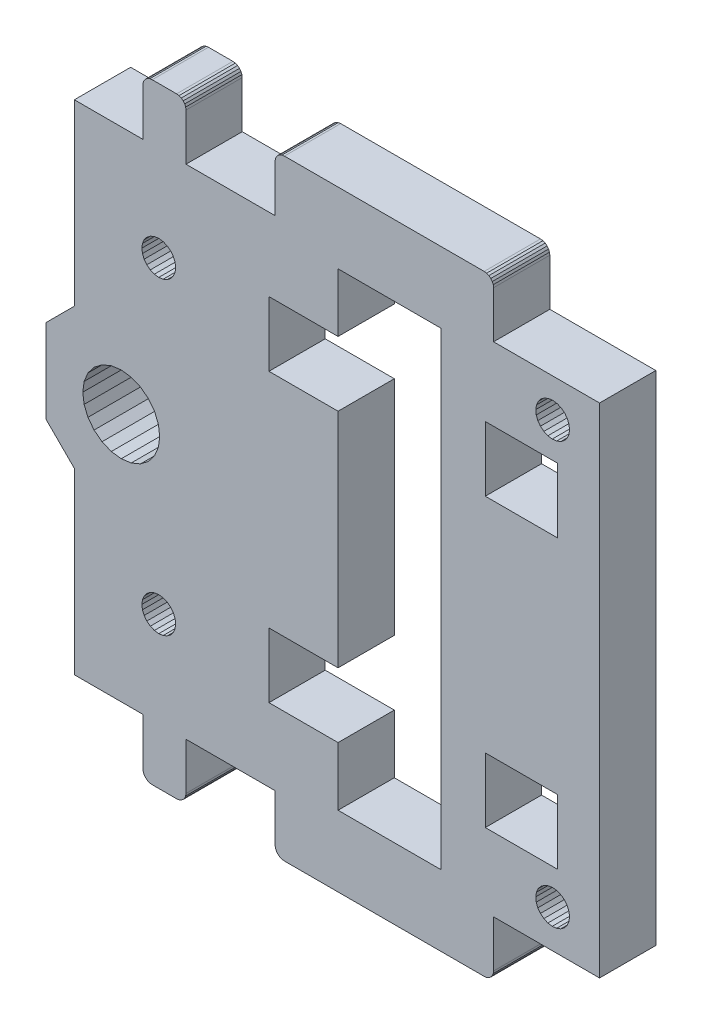
SolidWorks part; units mm, degrees
material "Maple"
ref_plane "Front Plane" through (0, 0, 0) normal (0, 0, 1) x (1, 0, 0)
ref_plane "Top Plane" through (0, 0, 0) normal (0, 1, 0) x (1, 0, 0)
ref_plane "Right Plane" through (0, 0, 0) normal (1, 0, 0) x (0, 0, -1)
sketch "Sketch1" plane through (0, 0, 0) normal (0, 0, 1) x (1, 0, 0)
  line L463 (-397.798, -104.5282) -> (-397.9876, -104.9582)
  line L464 (-397.9876, -104.9582) -> (-398.0594, -105.4226)
  line L465 (-398.0594, -105.4226) -> (-398.0086, -105.8897)
  line L466 (-398.0086, -105.8897) -> (-397.8386, -106.3278)
  line L467 (-397.8386, -106.3278) -> (-397.5611, -106.7069)
  line L468 (-397.5611, -106.7069) -> (-397.1948, -107.0013)
  line L469 (-397.1948, -107.0013) -> (-396.7648, -107.1909)
  line L470 (-396.7648, -107.1909) -> (-396.3005, -107.2627)
  line L471 (-396.3005, -107.2627) -> (-395.8333, -107.2119)
  line L472 (-395.8333, -107.2119) -> (-395.3953, -107.0419)
  line L473 (-395.3953, -107.0419) -> (-395.0161, -106.7643)
  line L474 (-395.0161, -106.7643) -> (-394.7217, -106.3981)
  line L475 (-394.7217, -106.3981) -> (-394.5322, -105.9681)
  line L476 (-394.5322, -105.9681) -> (-394.4603, -105.5037)
  line L477 (-394.4603, -105.5037) -> (-394.5112, -105.0366)
  line L478 (-425.7259, -95.9132) -> (-425.8258, -96.1543)
  line L479 (-439.92, -159.7726) -> (-439.82, -160.0136)
  line L480 (-439.82, -160.0136) -> (-439.661, -160.2205)
  line L481 (-439.661, -160.2205) -> (-439.454, -160.3793)
  line L482 (-446.3599, -127.9632) -> (-446.2202, -129.0243)
  line L483 (-438.2996, -129.0243) -> (-438.1599, -127.9632)
  line L484 (-443.321, -124.0029) -> (-444.3099, -124.4124)
  line L485 (-441.1987, -131.9234) -> (-440.2099, -131.5139)
  line L486 (-442.2599, -123.8632) -> (-443.321, -124.0029)
  line L487 (-440.2099, -124.4124) -> (-441.1987, -124.0029)
  line L488 (-438.7092, -130.0132) -> (-438.2996, -129.0243)
  line L489 (-450.2599, -132.4522) -> (-447.2599, -135.4522)
  line L490 (-450.2599, -123.4741) -> (-450.2599, -127.9351)
  line L491 (-450.2599, -123.4741) -> (-447.2599, -120.4741)
  line L492 (-447.2599, -120.4741) -> (-447.2599, -101.4132)
  line L493 (-403.0599, -95.5471) -> (-403.3011, -95.4472)
  line L494 (-402.594, -96.1543) -> (-402.6939, -95.9132)
  line L495 (-402.5599, -96.4132) -> (-402.594, -96.1543)
  line L496 (-439.217, -95.4472) -> (-438.9582, -95.4132)
  line L497 (-438.9582, -95.4132) -> (-436.3585, -95.4132)
  line L498 (-439.4582, -95.5471) -> (-439.217, -95.4472)
  line L499 (-425.8599, -159.5132) -> (-425.8599, -154.5132)
  line L500 (-425.8599, -159.5132) -> (-425.8258, -159.772)
  line L501 (-424.8599, -95.4132) -> (-425.1187, -95.4472)
  line L502 (-425.1187, -95.4472) -> (-425.3599, -95.5471)
  line L503 (-436.0996, -95.4472) -> (-436.3585, -95.4132)
  line L504 (-435.394, -159.772) -> (-435.4939, -160.0132)
  line L505 (-435.4939, -160.0132) -> (-435.6528, -160.2203)
  line L506 (-424.8599, -95.4132) -> (-403.5599, -95.4132)
  line L507 (-394.5112, -105.0366) -> (-394.6811, -104.5985)
  line L508 (-394.6811, -104.5985) -> (-394.9587, -104.2194)
  line L509 (-394.9587, -104.2194) -> (-395.325, -103.925)
  line L510 (-395.325, -103.925) -> (-395.7549, -103.7354)
  line L511 (-395.7549, -103.7354) -> (-396.2193, -103.6636)
  line L512 (-439.454, -160.3793) -> (-439.2129, -160.4791)
  line L513 (-439.2129, -160.4791) -> (-438.9542, -160.5132)
  line L514 (-403.3011, -95.4472) -> (-403.5599, -95.4132)
  line L515 (-395.0204, -151.7684) -> (-394.7248, -151.4031)
  line L516 (-394.7248, -151.4031) -> (-394.5338, -150.9738)
  line L517 (-394.5338, -150.9738) -> (-394.4605, -150.5097)
  line L518 (-394.4605, -150.5097) -> (-394.5098, -150.0424)
  line L519 (-394.5098, -150.0424) -> (-394.6783, -149.6037)
  line L520 (-394.6783, -149.6037) -> (-394.9546, -149.2237)
  line L521 (-394.9546, -149.2237) -> (-395.3199, -148.9281)
  line L522 (-395.3199, -148.9281) -> (-395.7492, -148.7371)
  line L523 (-395.7492, -148.7371) -> (-396.2134, -148.6638)
  line L524 (-396.2134, -148.6638) -> (-396.6807, -148.713)
  line L525 (-396.6807, -148.713) -> (-397.1193, -148.8816)
  line L526 (-397.1193, -148.8816) -> (-397.4994, -149.1579)
  line L527 (-397.4994, -149.1579) -> (-397.795, -149.5232)
  line L528 (-439.9986, -111.0473) -> (-440.0599, -111.5132)
  line L529 (-435.4924, -95.9132) -> (-435.6514, -95.706)
  line L530 (-435.6514, -95.706) -> (-435.8585, -95.5471)
  line L531 (-419.1424, -139.8132) -> (-419.1424, -116.1132)
  line L532 (-419.1424, -109.2132) -> (-419.1424, -102.9632)
  line L533 (-450.2636, -127.9632) -> (-450.2599, -127.9912)
  line L534 (-450.2599, -127.9912) -> (-450.2599, -132.4522)
  line L535 (-450.2599, -127.9351) -> (-450.2636, -127.9632)
  line L536 (-447.2599, -154.5132) -> (-447.2599, -135.4522)
  line L537 (-447.2599, -154.5132) -> (-439.9582, -154.5132)
  line L538 (-391.2599, -154.5132) -> (-402.5599, -154.5132)
  line L539 (-402.5599, -154.5132) -> (-402.5599, -159.5132)
  line L540 (-435.3599, -154.5132) -> (-435.3599, -159.5132)
  line L541 (-391.2599, -101.4132) -> (-391.2599, -154.5132)
  line L542 (-391.2599, -101.4132) -> (-402.5599, -101.4132)
  line L543 (-426.5109, -109.2132) -> (-426.5109, -116.1132)
  line L544 (-426.5109, -116.1132) -> (-419.1424, -116.1132)
  line L545 (-403.4424, -109.2132) -> (-403.4424, -116.1132)
  line L546 (-395.7424, -109.2132) -> (-403.4424, -109.2132)
  line L547 (-403.4424, -116.1132) -> (-395.7424, -116.1132)
  line L548 (-395.7424, -116.1132) -> (-395.7424, -109.2132)
  line L549 (-419.1424, -139.8132) -> (-426.5109, -139.8132)
  line L550 (-403.4424, -139.8132) -> (-403.4424, -146.7132)
  line L551 (-426.5109, -146.7132) -> (-419.1424, -146.7132)
  line L552 (-426.5109, -139.8132) -> (-426.5109, -146.7132)
  line L553 (-395.7424, -146.7132) -> (-395.7424, -139.8132)
  line L554 (-403.4424, -146.7132) -> (-395.7424, -146.7132)
  line L555 (-395.7424, -139.8132) -> (-403.4424, -139.8132)
  line L556 (-435.3599, -159.5132) -> (-435.394, -159.772)
  line L557 (-425.8258, -96.1543) -> (-425.8599, -96.4132)
  line L558 (-439.6653, -95.706) -> (-439.4582, -95.5471)
  line L559 (-439.8242, -95.9132) -> (-439.6653, -95.706)
  line L560 (-439.9241, -96.1543) -> (-439.8242, -95.9132)
  line L561 (-435.3925, -96.1543) -> (-435.4924, -95.9132)
  line L562 (-436.3599, -160.5132) -> (-438.9542, -160.5132)
  line L563 (-436.1011, -160.4791) -> (-436.3599, -160.5132)
  line L564 (-438.7258, -146.1518) -> (-438.2599, -146.2132)
  line L565 (-438.2599, -146.2132) -> (-437.794, -146.1518)
  line L566 (-437.794, -146.1518) -> (-437.3599, -145.972)
  line L567 (-437.3599, -145.972) -> (-436.9871, -145.6859)
  line L568 (-436.9871, -145.6859) -> (-436.701, -145.3132)
  line L569 (-436.701, -145.3132) -> (-436.5212, -144.879)
  line L570 (-436.5212, -144.879) -> (-436.4599, -144.4132)
  line L571 (-436.4599, -144.4132) -> (-436.5212, -143.9473)
  line L572 (-436.5212, -143.9473) -> (-436.701, -143.5132)
  line L573 (-436.701, -143.5132) -> (-436.9871, -143.1404)
  line L574 (-436.9871, -143.1404) -> (-437.3599, -142.8543)
  line L575 (-437.3599, -142.8543) -> (-437.794, -142.6745)
  line L576 (-437.794, -142.6745) -> (-438.2599, -142.6132)
  line L577 (-438.2599, -142.6132) -> (-438.7258, -142.6745)
  line L578 (-402.6939, -95.9132) -> (-402.8528, -95.706)
  line L579 (-435.6528, -160.2203) -> (-435.8599, -160.3792)
  line L580 (-435.8599, -160.3792) -> (-436.1011, -160.4791)
  line L581 (-402.5599, -101.4132) -> (-402.5599, -96.4132)
  line L582 (-447.2599, -101.4132) -> (-439.9582, -101.4132)
  line L583 (-425.8599, -101.4132) -> (-425.8599, -96.4132)
  line L584 (-436.701, -110.6132) -> (-436.9871, -110.2404)
  line L585 (-436.9871, -110.2404) -> (-437.3599, -109.9543)
  line L586 (-437.3599, -109.9543) -> (-437.794, -109.7745)
  line L587 (-437.794, -109.7745) -> (-438.2599, -109.7132)
  line L588 (-438.2599, -109.7132) -> (-438.7258, -109.7745)
  line L589 (-438.7258, -109.7745) -> (-439.1599, -109.9543)
  line L590 (-439.1599, -109.9543) -> (-439.5327, -110.2404)
  line L591 (-439.5327, -110.2404) -> (-439.8187, -110.6132)
  line L592 (-439.8187, -110.6132) -> (-439.9986, -111.0473)
  line L593 (-396.2193, -103.6636) -> (-396.6864, -103.7144)
  line L594 (-396.6864, -103.7144) -> (-397.1245, -103.8844)
  line L595 (-397.1245, -103.8844) -> (-397.5037, -104.162)
  line L596 (-397.5037, -104.162) -> (-397.798, -104.5282)
  line L597 (-403.5599, -160.5132) -> (-424.8599, -160.5132)
  line L598 (-440.0599, -111.5132) -> (-439.9986, -111.979)
  line L599 (-439.9986, -111.979) -> (-439.8187, -112.4132)
  line L600 (-439.8187, -112.4132) -> (-439.5327, -112.7859)
  line L601 (-439.5327, -112.7859) -> (-439.1599, -113.072)
  line L602 (-439.1599, -113.072) -> (-438.7258, -113.2518)
  line L603 (-438.7258, -113.2518) -> (-438.2599, -113.3132)
  line L604 (-438.2599, -113.3132) -> (-437.794, -113.2518)
  line L605 (-437.794, -113.2518) -> (-437.3599, -113.072)
  line L606 (-437.3599, -113.072) -> (-436.9871, -112.7859)
  line L607 (-436.9871, -112.7859) -> (-436.701, -112.4132)
  line L608 (-436.701, -112.4132) -> (-436.5212, -111.979)
  line L609 (-436.5212, -111.979) -> (-436.4599, -111.5132)
  line L610 (-436.4599, -111.5132) -> (-436.5212, -111.0473)
  line L611 (-436.5212, -111.0473) -> (-436.701, -110.6132)
  line L612 (-425.567, -95.706) -> (-425.7259, -95.9132)
  line L613 (-435.3585, -96.4132) -> (-435.3925, -96.1543)
  line L614 (-435.8585, -95.5471) -> (-436.0996, -95.4472)
  line L615 (-408.1424, -152.9631) -> (-419.1424, -152.9631)
  line L616 (-408.1424, -102.9632) -> (-408.1424, -152.9631)
  line L617 (-419.1424, -102.9632) -> (-408.1424, -102.9632)
  line L618 (-419.1424, -152.9631) -> (-419.1424, -146.7132)
  line L619 (-438.2996, -126.902) -> (-438.7092, -125.9132)
  line L620 (-438.7092, -125.9132) -> (-439.3607, -125.064)
  line L621 (-439.3607, -125.064) -> (-440.2099, -124.4124)
  line L622 (-441.1987, -124.0029) -> (-442.2599, -123.8632)
  line L623 (-444.3099, -124.4124) -> (-445.159, -125.064)
  line L624 (-445.159, -125.064) -> (-445.8106, -125.9132)
  line L625 (-445.8106, -125.9132) -> (-446.2202, -126.902)
  line L626 (-446.2202, -126.902) -> (-446.3599, -127.9632)
  line L627 (-446.2202, -129.0243) -> (-445.8106, -130.0132)
  line L628 (-445.8106, -130.0132) -> (-445.159, -130.8623)
  line L629 (-445.159, -130.8623) -> (-444.3099, -131.5139)
  line L630 (-444.3099, -131.5139) -> (-443.321, -131.9234)
  line L631 (-443.321, -131.9234) -> (-442.2599, -132.0632)
  line L632 (-442.2599, -132.0632) -> (-441.1987, -131.9234)
  line L633 (-440.2099, -131.5139) -> (-439.3607, -130.8623)
  line L634 (-439.3607, -130.8623) -> (-438.7092, -130.0132)
  line L635 (-438.1599, -127.9632) -> (-438.2996, -126.902)
  line L636 (-419.1424, -109.2132) -> (-426.5109, -109.2132)
  line L637 (-425.3599, -160.3792) -> (-425.1187, -160.4791)
  line L638 (-425.1187, -160.4791) -> (-424.8599, -160.5132)
  line L639 (-403.5599, -160.5132) -> (-403.3011, -160.4791)
  line L640 (-402.8528, -95.706) -> (-403.0599, -95.5471)
  line L641 (-438.7258, -142.6745) -> (-439.1599, -142.8543)
  line L642 (-439.1599, -142.8543) -> (-439.5327, -143.1404)
  line L643 (-439.5327, -143.1404) -> (-439.8187, -143.5132)
  line L644 (-397.795, -149.5232) -> (-397.9859, -149.9525)
  line L645 (-397.9859, -149.9525) -> (-398.0593, -150.4166)
  line L646 (-398.0593, -150.4166) -> (-398.01, -150.8839)
  line L647 (-398.01, -150.8839) -> (-397.8415, -151.3226)
  line L648 (-397.8415, -151.3226) -> (-397.5651, -151.7026)
  line L649 (-397.5651, -151.7026) -> (-397.1999, -151.9982)
  line L650 (-397.1999, -151.9982) -> (-396.7705, -152.1892)
  line L651 (-396.7705, -152.1892) -> (-396.3064, -152.2625)
  line L652 (-396.3064, -152.2625) -> (-395.8391, -152.2133)
  line L653 (-395.8391, -152.2133) -> (-395.4005, -152.0447)
  line L654 (-395.4005, -152.0447) -> (-395.0204, -151.7684)
  line L655 (-425.8258, -159.772) -> (-425.7259, -160.0132)
  line L656 (-425.7259, -160.0132) -> (-425.567, -160.2203)
  line L657 (-425.567, -160.2203) -> (-425.3599, -160.3792)
  line L658 (-403.3011, -160.4791) -> (-403.0599, -160.3792)
  line L659 (-439.9542, -159.5139) -> (-439.92, -159.7726)
  line L660 (-402.594, -159.772) -> (-402.5599, -159.5132)
  line L661 (-403.0599, -160.3792) -> (-402.8528, -160.2203)
  line L662 (-402.8528, -160.2203) -> (-402.6939, -160.0132)
  line L663 (-425.3599, -95.5471) -> (-425.567, -95.706)
  line L664 (-439.9582, -96.4132) -> (-439.9241, -96.1543)
  line L665 (-435.3585, -96.4132) -> (-435.3585, -101.4132)
  line L666 (-402.6939, -160.0132) -> (-402.594, -159.772)
  line L667 (-439.8187, -143.5132) -> (-439.9986, -143.9473)
  line L668 (-439.9986, -143.9473) -> (-440.0599, -144.4132)
  line L669 (-440.0599, -144.4132) -> (-439.9986, -144.879)
  line L670 (-439.9986, -144.879) -> (-439.8187, -145.3132)
  line L671 (-439.8187, -145.3132) -> (-439.5327, -145.6859)
  line L672 (-439.5327, -145.6859) -> (-439.1599, -145.972)
  line L673 (-439.1599, -145.972) -> (-438.7258, -146.1518)
  line L674 (-439.9582, -101.4132) -> (-439.9582, -96.4132)
  line L675 (-435.3585, -101.4132) -> (-425.8599, -101.4132)
  line L676 (-439.9582, -154.5132) -> (-439.9542, -159.5139)
  line L677 (-435.3599, -154.5132) -> (-425.8599, -154.5132)
  line L8707 (-430.2329, -128.6953) -> (-430.2329, -129.0013)
  line L8708 (-430.2329, -129.0013) -> (-430.2128, -129.0975)
  line L8709 (-430.2128, -129.0975) -> (-430.1525, -129.1862)
  line L8710 (-430.1525, -129.1862) -> (-429.9114, -129.3415)
  line L8711 (-429.9114, -129.3415) -> (-429.55, -129.4469)
  line L8712 (-429.55, -129.4469) -> (-429.109, -129.482)
  line L8713 (-429.109, -129.482) -> (-428.668, -129.4469)
  line L8714 (-428.668, -129.4469) -> (-428.3067, -129.3415)
  line L8715 (-428.3067, -129.3415) -> (-428.0655, -129.1862)
  line L8716 (-428.0655, -129.1862) -> (-428.0052, -129.0975)
  line L8717 (-428.0052, -129.0975) -> (-427.9851, -129.0013)
  line L8718 (-427.9851, -129.0013) -> (-427.9726, -127.7276)
  line L8719 (-427.9726, -127.7276) -> (-428.029, -127.4759)
  line L8720 (-428.029, -127.4759) -> (-428.192, -127.2953)
  line L8721 (-428.192, -127.2953) -> (-428.4614, -127.1856)
  line L8722 (-428.4614, -127.1856) -> (-428.8374, -127.147)
  line L8723 (-428.8374, -127.147) -> (-429.5188, -127.1298)
  line L8724 (-429.5188, -127.1298) -> (-429.8458, -127.0908)
  line L8725 (-429.8458, -127.0908) -> (-430.1361, -126.9269)
  line L8726 (-430.1361, -126.9269) -> (-430.2087, -126.8298)
  line L8727 (-430.2087, -126.8298) -> (-430.2329, -126.7224)
  line L8728 (-430.2329, -126.7224) -> (-430.2329, -125.6548)
  line L8729 (-430.2329, -125.6548) -> (-430.2128, -125.5587)
  line L8730 (-430.2128, -125.5587) -> (-430.1525, -125.4699)
  line L8731 (-430.1525, -125.4699) -> (-429.9114, -125.3146)
  line L8732 (-429.9114, -125.3146) -> (-429.55, -125.2092)
  line L8733 (-429.55, -125.2092) -> (-429.109, -125.1741)
  line L8734 (-429.109, -125.1741) -> (-428.668, -125.2092)
  line L8735 (-428.668, -125.2092) -> (-428.3067, -125.3146)
  line L8736 (-428.3067, -125.3146) -> (-428.0655, -125.4699)
  line L8737 (-428.0655, -125.4699) -> (-428.0052, -125.5587)
  line L8738 (-428.0052, -125.5587) -> (-427.9851, -125.6548)
  line L8739 (-427.9851, -125.6548) -> (-427.9851, -125.9608)
  line L8740 (-427.9851, -125.9608) -> (-427.9851, -125.6548)
  line L8741 (-427.9851, -125.6548) -> (-428.0052, -125.5587)
  line L8742 (-428.0052, -125.5587) -> (-428.0655, -125.4699)
  line L8743 (-428.0655, -125.4699) -> (-428.3067, -125.3146)
  line L8744 (-428.3067, -125.3146) -> (-428.668, -125.2092)
  line L8745 (-428.668, -125.2092) -> (-429.109, -125.1741)
  line L8746 (-429.109, -125.1741) -> (-429.55, -125.2092)
  line L8747 (-429.55, -125.2092) -> (-429.9114, -125.3146)
  line L8748 (-429.9114, -125.3146) -> (-430.1525, -125.4699)
  line L8749 (-430.1525, -125.4699) -> (-430.2128, -125.5587)
  line L8750 (-430.2128, -125.5587) -> (-430.2329, -125.6548)
  line L8751 (-430.2329, -125.6548) -> (-430.2329, -126.7224)
  line L8752 (-430.2329, -126.7224) -> (-430.2087, -126.8298)
  line L8753 (-430.2087, -126.8298) -> (-430.1361, -126.9269)
  line L8754 (-430.1361, -126.9269) -> (-429.8458, -127.0908)
  line L8755 (-429.8458, -127.0908) -> (-429.5188, -127.1298)
  line L8756 (-429.5188, -127.1298) -> (-428.8374, -127.147)
  line L8757 (-428.8374, -127.147) -> (-428.4614, -127.1856)
  line L8758 (-428.4614, -127.1856) -> (-428.192, -127.2953)
  line L8759 (-428.192, -127.2953) -> (-428.029, -127.4759)
  line L8760 (-428.029, -127.4759) -> (-427.9726, -127.7276)
  line L8761 (-427.9726, -127.7276) -> (-427.9851, -129.0013)
  line L8762 (-427.9851, -129.0013) -> (-428.0052, -129.0975)
  line L8763 (-428.0052, -129.0975) -> (-428.0655, -129.1862)
  line L8764 (-428.0655, -129.1862) -> (-428.3067, -129.3415)
  line L8765 (-428.3067, -129.3415) -> (-428.668, -129.4469)
  line L8766 (-428.668, -129.4469) -> (-429.109, -129.482)
  line L8767 (-429.109, -129.482) -> (-429.55, -129.4469)
  line L8768 (-429.55, -129.4469) -> (-429.9114, -129.3415)
  line L8769 (-429.9114, -129.3415) -> (-430.1525, -129.1862)
  line L8770 (-430.1525, -129.1862) -> (-430.2128, -129.0975)
  line L8771 (-430.2128, -129.0975) -> (-430.2329, -129.0013)
  line L8772 (-430.2329, -129.0013) -> (-430.2329, -128.6953)
extrude "Boss-Extrude1" add sketch "Sketch1" along normal blind 6
